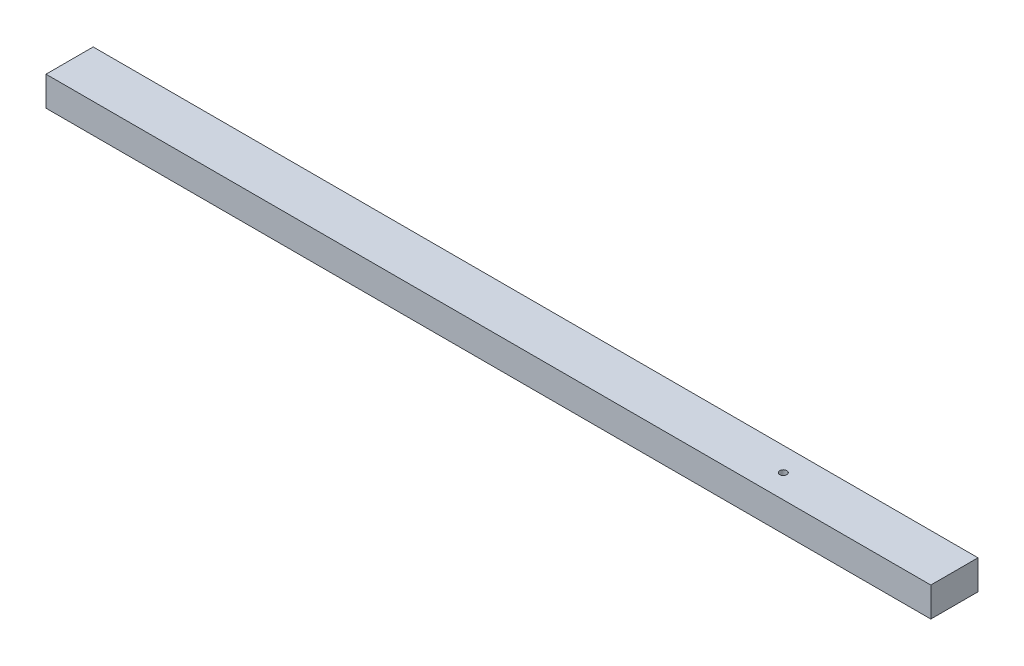
SolidWorks part; units mm, degrees
ref_plane "Спереди" through (0, 0, 0) normal (0, 0, 1) x (1, 0, 0)
ref_plane "Сверху" through (0, 0, 0) normal (0, 1, 0) x (1, 0, 0)
ref_plane "Справа" through (0, 0, 0) normal (1, 0, 0) x (0, 0, -1)
sketch "Эскиз1" plane through (0, 0, 0) normal (1, 0, 0) x (0, 0, -1)
  line L1 (0, 0) -> (80, 0)
  line L2 (0, 0) -> (0, 50)
  line L3 (0, 50) -> (80, 50)
  line L4 (80, 0) -> (80, 50)
extrude "Бобышка-Вытянуть1" add sketch "Эскиз1" along normal blind 1500
sketch "Эскиз2" plane through (0, 50, 0) normal (0, 1, 0) x (1, 0, 0)
  circle A0 centre (1210, 40) radius 6
extrude "Вырез-Вытянуть1" cut sketch "Эскиз2" against normal through all
